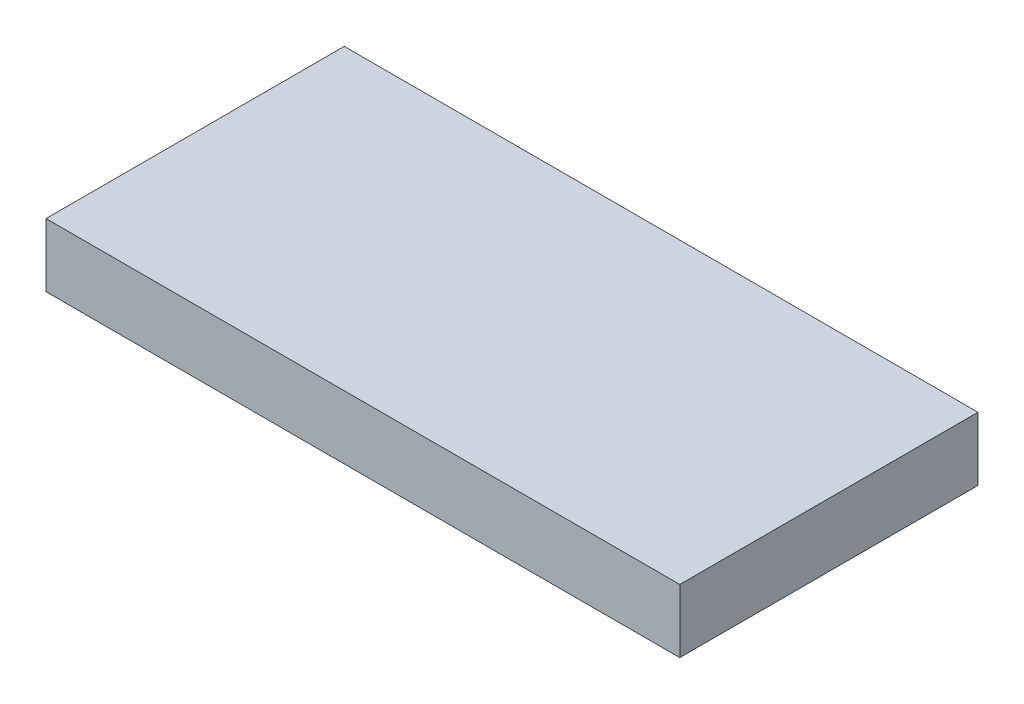
SolidWorks part; units mm, degrees
ref_plane "Alzado" through (0, 0, 0) normal (0, 0, 1) x (1, 0, 0)
ref_plane "Planta" through (0, 0, 0) normal (0, 1, 0) x (1, 0, 0)
ref_plane "Vista lateral" through (0, 0, 0) normal (1, 0, 0) x (0, 0, -1)
sketch "Croquis1" plane through (0, 0, 0) normal (0, 1, 0) x (1, 0, 0)
  line L1 (-24.5619, -7.9752) -> (-7.5619, -7.9752)
  line L2 (-24.5619, -7.9752) -> (-24.5619, -15.9752)
  line L3 (-24.5619, -15.9752) -> (-7.5619, -15.9752)
  line L4 (-7.5619, -7.9752) -> (-7.5619, -15.9752)
  dimension "D1" = 17
  dimension "D2" = 8
  dimension "D3" = 17
  dimension "D4" = 8
extrude "Saliente-Extruir1" add sketch "Croquis1" along normal blind 1.7
